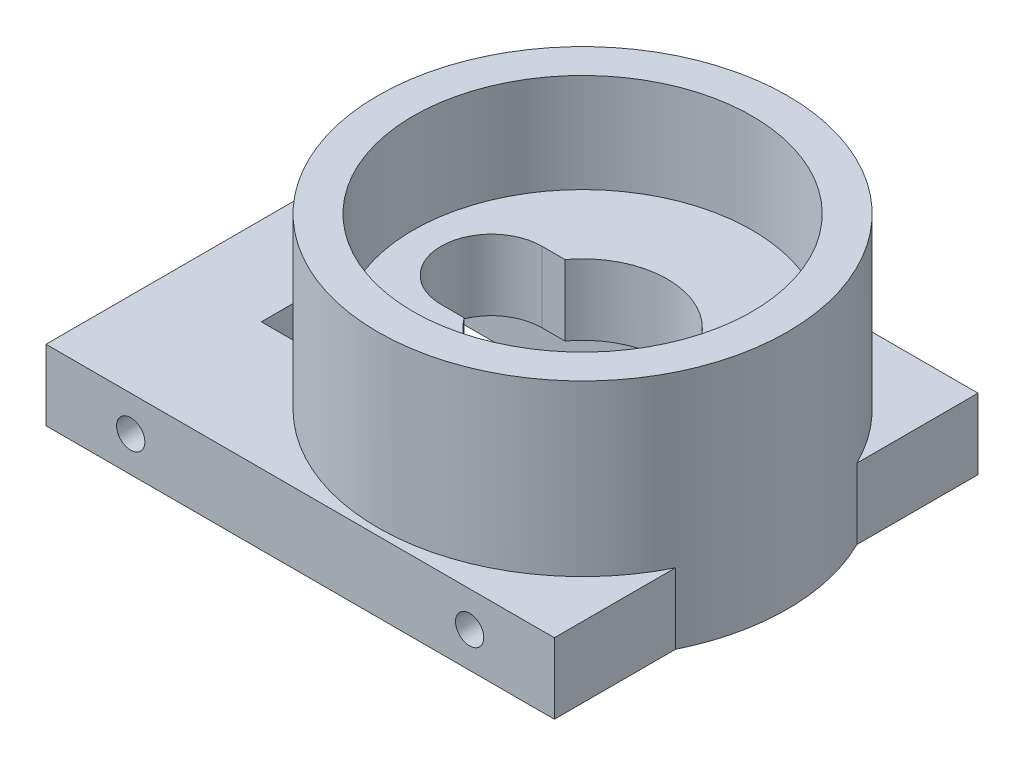
SolidWorks part; units mm, degrees
ref_plane "前视基准面" through (0, 0, 0) normal (0, 0, 1) x (1, 0, 0)
ref_plane "上视基准面" through (0, 0, 0) normal (0, 1, 0) x (1, 0, 0)
ref_plane "右视基准面" through (0, 0, 0) normal (1, 0, 0) x (0, 0, -1)
sketch "草图1" plane through (0, 0, 0) normal (0, 1, 0) x (1, 0, 0)
  line L1 (-18, 15) -> (18, 15)
  line L2 (-18, 15) -> (-18, -15)
  line L3 (-18, -15) -> (18, -15)
  line L4 (18, 15) -> (18, -15)
  line L5 (-18, 15) -> (18, -15) construction
  line L6 (-18, -15) -> (18, 15) construction
  point P0 (0, 0)
  dimension "D1" = 30
  dimension "D2" = 36
extrude "凸台-拉伸1" add sketch "草图1" along normal blind 5
sketch "草图2" plane through (0, 0, 0) normal (0, -1, 0) x (1, 0, 0)
  circle A0 centre (5, 0) radius 14.5
  dimension "D1" = 29
  dimension "D2" = 5
extrude "凸台-拉伸2" add sketch "草图2" against normal blind 17
sketch "草图4" plane through (0, 0, 0) normal (0, -1, 0) x (1, 0, 0)
  line L1 (-16.5, 6) -> (16.5, 6)
  line L2 (-16.5, 6) -> (-16.5, -6)
  line L3 (-16.5, -6) -> (16.5, -6)
  line L4 (16.5, 6) -> (16.5, -6)
  line L5 (-16.5, 6) -> (16.5, -6) construction
  line L6 (-16.5, -6) -> (16.5, 6) construction
  point P0 (0, 0)
  dimension "D1" = 33
  dimension "D2" = 12
extrude "切除-拉伸2" cut sketch "草图4" against normal blind 2
sketch "草图8" plane through (0, 2, 0) normal (0, -1, 0) x (1, 0, 0)
  line L0 (0, -1000) -> (0, 49000) construction
  circle A0 centre (14, 0) radius 1
  circle A1 centre (-14, 0) radius 1
  dimension "D1" = 28
  dimension "D2" = 2
extrude "切除-拉伸6" cut sketch "草图8" against normal blind 3
sketch "草图5" plane through (0, 2, 0) normal (0, -1, 0) x (1, 0, 0)
  line L0 (16.5, 6) -> (-16.5, 6) construction
  line L1 (-11.75, -6) -> (11.75, -6)
  line L2 (-11.75, -6) -> (-11.75, 6)
  line L3 (-11.75, 6) -> (11.75, 6)
  line L4 (11.75, -6) -> (11.75, 6)
  line L5 (-11.75, -6) -> (11.75, 6) construction
  line L6 (-11.75, 6) -> (11.75, -6) construction
  point P0 (0, 0)
  dimension "D1" = 23.5
extrude "切除-拉伸3" cut sketch "草图5" against normal up to surface (3 mm away) and the other way through all up to face at (-14, 5, -1)
sketch "草图3" plane through (0, 17, 0) normal (0, 1, 0) x (1, 0, 0)
  circle A0 centre (5, 0) radius 12
  dimension "D1" = 24
extrude "切除-拉伸1" cut sketch "草图3" against normal blind 7
sketch "草图6" plane through (0, 10, 0) normal (0, 1, 0) x (1, 0, 0)
  circle A0 centre (5, 0) radius 6
  dimension "D1" = 12
extrude "切除-拉伸4" cut sketch "草图6" against normal up to surface (5 mm away) up to face at (-0.4168, 5, 0)
sketch "草图7" plane through (0, 10, 0) normal (0, 1, 0) x (1, 0, 0)
  line L0 (-1.4555, 3.5709) -> (2.1154, 3.5709)
  line L1 (2.1154, 3.5709) -> (2.1154, -3.5709)
  line L2 (2.1154, -3.5709) -> (-1.4555, -3.5709)
  arc A0 (-1.4555, 3.5709) -> (-1.4555, -3.5709) centre (-1.4555, 0) ccw
extrude "切除-拉伸5" cut sketch "草图7" against normal up to surface (5 mm away) up to face at (-0.4168, 5, 0)
sketch "草图9" plane through (0, 0, -15) normal (0, 0, -1) x (-1, 0, 0)
  line L0 (-1000, 2.5) -> (49000, 2.5) construction
  line L2 (-18, 5) -> (18, 0) construction
  line L3 (18, 5) -> (-18, 0) construction
  line L4 (0, -997.25) -> (0, 49002.75) construction
  circle A0 centre (12, 2.5) radius 1
  circle A1 centre (-12, 2.5) radius 1
  point P7 (0, 2.5)
  dimension "D1" = 2
  dimension "D2" = 12
extrude "切除-拉伸7" cut sketch "草图9" against normal blind 5
mirror "镜向1" about plane through (0, 0, 0) normal (0, 0, 1) of "切除-拉伸7"
